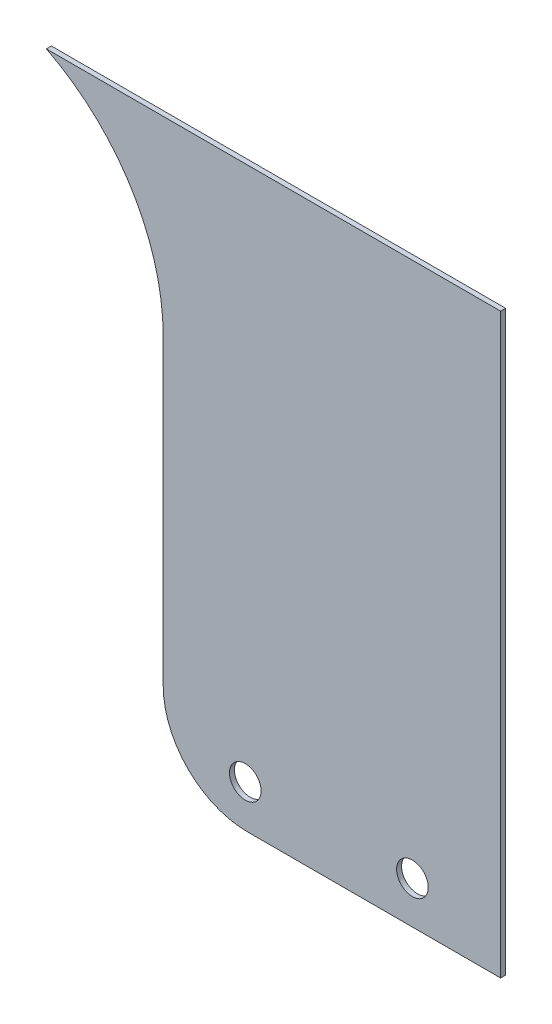
SolidWorks part; units mm, degrees
ref_plane "Front Plane" through (0, 0, 0) normal (0, 0, 1) x (1, 0, 0)
ref_plane "Top Plane" through (0, 0, 0) normal (0, 1, 0) x (1, 0, 0)
ref_plane "Right Plane" through (0, 0, 0) normal (1, 0, 0) x (0, 0, -1)
sketch "Sketch1" plane through (0, 0, 165.1) normal (0, 0, 1) x (1, 0, 0)
  line L0 (-418.175, 962.43) -> (-584.2, 962.43) construction
  line L1 (-418.175, 962.43) -> (-554.9557, 962.43)
  line L2 (-418.175, 962.43) -> (-418.175, 788.53)
  line L3 (-418.175, 788.53) -> (-494.375, 788.53)
  line L4 (-519.775, 813.93) -> (-519.775, 905.0248)
  line L5 (-375.1, 788.53) -> (-418.175, 788.53) construction
  line L6 (-584.2, 905.0248) -> (-519.775, 905.0248) construction
  line L7 (-356.05, 805.9925) -> (-444.7375, 805.9925) construction
  line L8 (-449.5, 780) -> (-449.5, 812.8) construction
  line L9 (-490.3, 812.8) -> (-490.3, 780) construction
  arc A0 (-519.775, 905.0248) -> (-554.9557, 962.43) centre (-584.2, 905.0248) ccw
  circle A1 centre (-444.7375, 801.23) radius 4.7625
  circle A2 centre (-495.0625, 801.23) radius 4.7625
  circle A3 centre (-356.05, 801.23) radius 4.7625 construction
  circle A4 centre (-356.05, 801.23) radius 4.7625 construction
  arc A6 (-494.375, 788.53) -> (-519.775, 813.93) centre (-494.375, 813.93) cw
  point P25 (-519.775, 788.53)
  dimension "D3" = 25.4
  dimension "D1" = 101.6
  dimension "D2" = 173.9
extrude "Extrude1" add sketch "Sketch1" along normal blind 1.5
